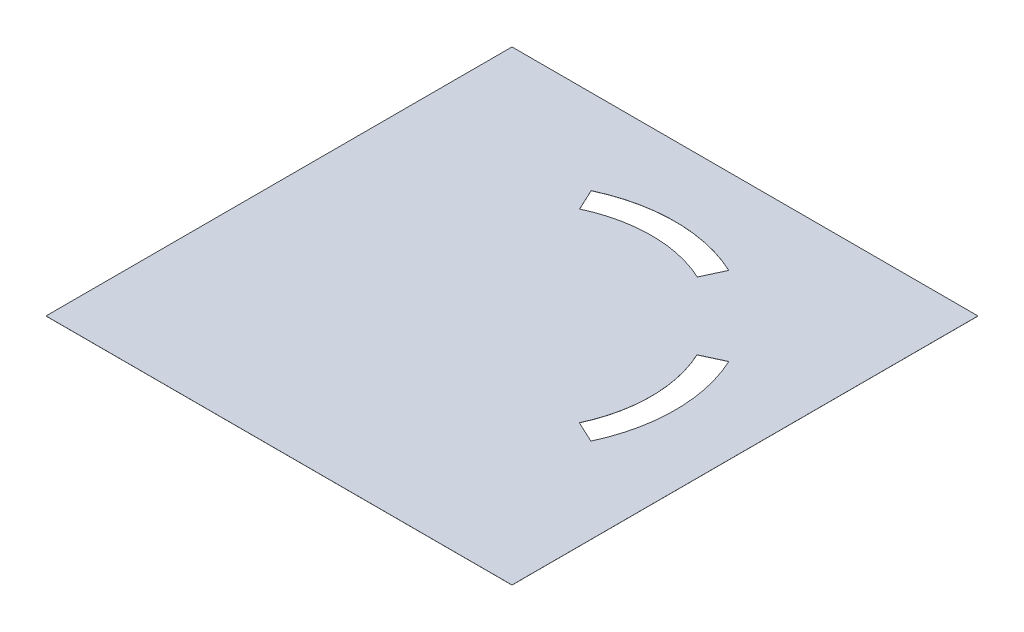
SolidWorks part; units mm, degrees
ref_plane "Front Plane" through (0, 0, 0) normal (0, 0, 1) x (1, 0, 0)
ref_plane "Top Plane" through (0, 0, 0) normal (0, 1, 0) x (1, 0, 0)
ref_plane "Right Plane" through (0, 0, 0) normal (1, 0, 0) x (0, 0, -1)
sketch "Sketch1" plane through (0, 0, 0) normal (0, 1, 0) x (1, 0, 0)
  line L0 (0, 0) -> (0, 107.07)
  line L1 (0, 0) -> (107.07, 0)
  line L2 (0, 107.07) -> (107.07, 107.07)
  line L3 (107.07, 107.07) -> (107.07, 0)
  line L10 (40.021, 82.5764) -> (37.6953, 87.5639)
  line L13 (67.0772, 82.5764) -> (69.3747, 87.5034)
  line L14 (82.5187, 67.0503) -> (87.5034, 69.3747)
  line L15 (82.5187, 40.0197) -> (87.5034, 37.6953)
  arc A0 (37.6953, 87.5639) -> (69.3747, 87.5034) centre (53.4708, 53.8846) cw
  arc A1 (40.021, 82.5764) -> (67.0772, 82.5764) centre (53.5491, 53.5652) cw
  arc A2 (82.5187, 67.0503) -> (82.5187, 40.0197) centre (53.535, 53.535) cw
  arc A3 (87.5034, 69.3747) -> (87.5034, 37.6953) centre (53.535, 53.535) cw
extrude "Boss-Extrude1" add sketch "Sketch1" along normal blind 0.02
scale "Scale1" bodies to scale 101 scale about centroid uniform scaling yes scale factor 0.5
